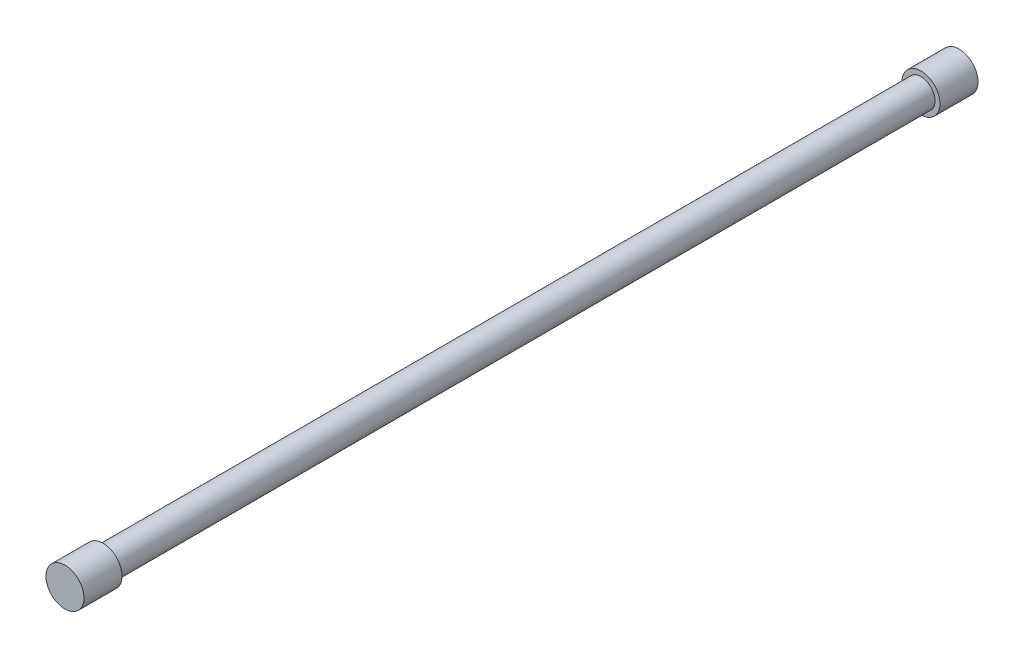
SolidWorks part; units mm, degrees
ref_plane "Front Plane" through (0, 0, 0) normal (0, 0, 1) x (1, 0, 0)
ref_plane "Top Plane" through (0, 0, 0) normal (0, 1, 0) x (1, 0, 0)
ref_plane "Right Plane" through (0, 0, 0) normal (1, 0, 0) x (0, 0, -1)
sketch "Sketch1" plane through (0, 0, 0) normal (0, 0, 1) x (1, 0, 0)
  circle A0 centre (0, 0) radius 7.41
  dimension "D1" = 14.82
extrude "Boss-Extrude1" add sketch "Sketch1" against normal blind 430
sketch "Sketch2" plane through (0, 0, -430) normal (0, 0, -1) x (-1, 0, 0)
  circle A0 centre (0, 0) radius 10
  dimension "D1" = 20
extrude "Boss-Extrude2" add sketch "Sketch2" along normal blind 20
sketch "Sketch3" plane through (0, 0, 0) normal (0, 0, 1) x (1, 0, 0)
  circle A0 centre (0, 0) radius 10
  dimension "D1" = 20
extrude "Boss-Extrude3" add sketch "Sketch3" along normal blind 20
